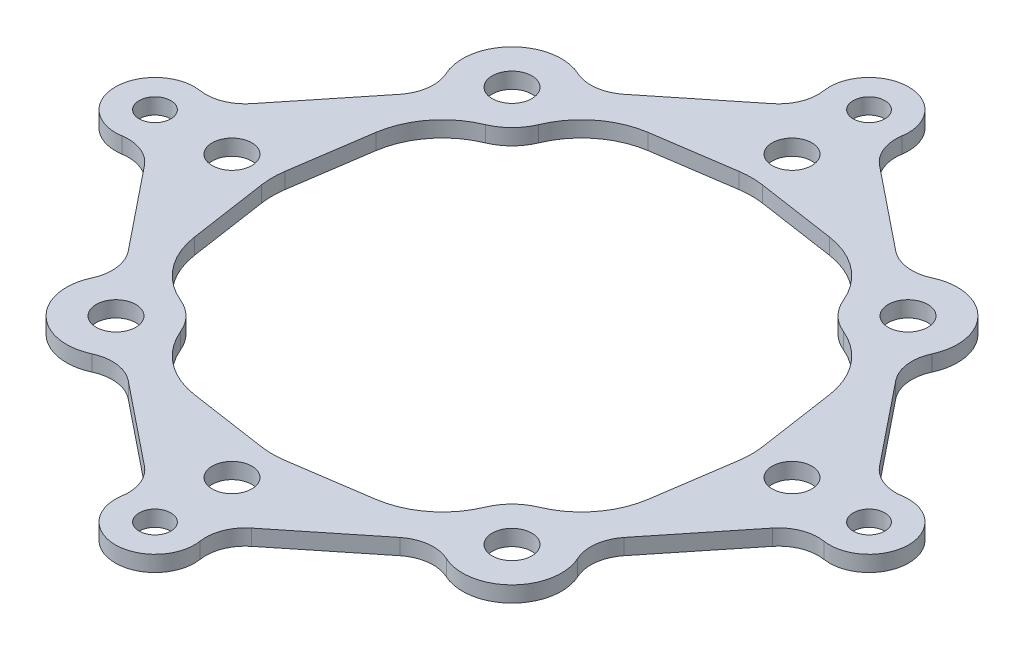
SolidWorks part; units mm, degrees
ref_plane "前视基准面" through (0, 0, 0) normal (0, 0, 1) x (1, 0, 0)
ref_plane "上视基准面" through (0, 0, 0) normal (0, 1, 0) x (1, 0, 0)
ref_plane "右视基准面" through (0, 0, 0) normal (1, 0, 0) x (0, 0, -1)
sketch "草图1" plane through (0, 0, 0) normal (0, 1, 0) x (1, 0, 0)
  line L13 (7.6123, 18.0495) -> (2.8008, 24.921)
  line L70 (0, 24.921) -> (0, 18.8312)
  line L96 (0, 0) -> (1, 1)
  line L104 (0, 24.921) -> (2.8008, 24.921)
  line L116 (8.0508, 11.5654) -> (1.5594, 16.7789)
  line L130 (0, 17.2312) -> (0, 15.1421)
  line L133 (8.2322, 8.2322) -> (9.2929, 9.2929)
  line L135 (10.7071, 10.7071) -> (11.7678, 11.7678)
  line L136 (0, 13.1421) -> (0, 12.1421)
  line L137 (0, 12.1421) -> (7.7087, 11)
  arc A122 (0, 17.2312) -> (0, 18.8312) centre (0, 18.0312) ccw
  arc A129 (0, 13.1421) -> (0, 15.1421) centre (0, 14.1421) ccw
  arc A131 (7.7087, 11) -> (8.2322, 8.2322) centre (10, 10) ccw
  arc A132 (7.7087, 11) -> (8.2322, 8.2322) centre (10, 10) ccw
  arc A133 (1.5594, 16.7789) -> (0, 20.0312) centre (0, 18.0312) ccw
  arc A134 (10.7071, 10.7071) -> (9.2929, 9.2929) centre (10, 10) ccw
  arc A135 (11.7678, 11.7678) -> (8.0508, 11.5654) centre (10, 10) ccw
  arc A136 (7.7087, 11) -> (8.2322, 8.2322) centre (10, 10) ccw
extrude "凸台-拉伸1" add sketch "草图1" along normal blind 0.8
mirror "镜向1" about plane through (0, 0.8, 0) normal (-0.7071, 0, -0.7071) of "凸台-拉伸1"
mirror "镜向2" about plane through (0, 0.8, 0) normal (1, 0, 0) of bodies 123
mirror "镜向3" about plane through (0, 0.8, 0) normal (0, 0, 1) of bodies 124
fillet "圆角1" radius 4 12 edges at (12.1421, 0.4, 0) (11, 0.4, -7.7087) (0, 0.4, -12.1421) (-7.7087, 0.4, -11) (-11, 0.4, -7.7087) (-12.1421, 0.4, 0) (-11, 0.4, 7.7087) (-7.7087, 0.4, 11) (0, 0.4, 12.1421) (7.7087, 0.4, 11) (11, 0.4, 7.7087) (7.7087, 0.4, -11)
fillet "圆角2" radius 2 16 edges at (11.5654, 0.4, 8.0508) (8.0508, 0.4, 11.5654) (1.5594, 0.4, 16.7789) (-1.5594, 0.4, 16.7789) (-8.0508, 0.4, 11.5654) (-11.5654, 0.4, 8.0508) (-16.7789, 0.4, 1.5594) (-16.7789, 0.4, -1.5594) (-11.5654, 0.4, -8.0508) (-8.0508, 0.4, -11.5654) (-1.5594, 0.4, -16.7789) (1.5594, 0.4, -16.7789) (8.0508, 0.4, -11.5654) (16.7789, 0.4, -1.5594) (16.7789, 0.4, 1.5594) (11.5654, 0.4, -8.0508)
